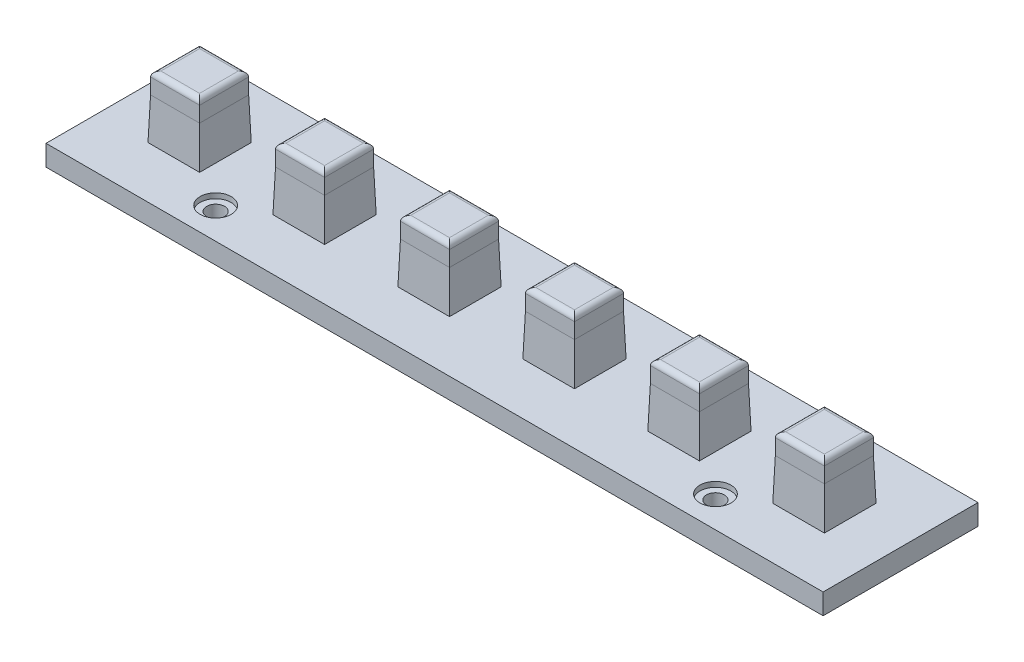
SolidWorks part; units mm, degrees
ref_plane "Front Plane" through (0, 0, 0) normal (0, 0, 1) x (1, 0, 0)
ref_plane "Top Plane" through (0, 0, 0) normal (0, 1, 0) x (1, 0, 0)
ref_plane "Right Plane" through (0, 0, 0) normal (1, 0, 0) x (0, 0, -1)
sketch "Sketch1" plane through (0, 0, 0) normal (0, 1, 0) x (1, 0, 0)
  line L0 (0, 15) -> (14.75, 15) construction
  line L1 (0, 0) -> (150.5, 0)
  line L2 (0, 0) -> (0, 30)
  line L3 (0, 30) -> (150.5, 30)
  line L4 (150.5, 0) -> (150.5, 30)
  line L5 (0, 0) -> (150.5, 30) construction
  line L6 (0, 30) -> (150.5, 0) construction
  line L7 (14.75, 15) -> (38.95, 15) construction
  line L8 (38.95, 15) -> (63.15, 15) construction
  line L9 (63.15, 15) -> (87.35, 15) construction
  line L10 (87.35, 15) -> (111.55, 15) construction
  line L11 (111.55, 15) -> (135.75, 15) construction
  line L14 (10, 19.75) -> (19.5, 19.75)
  line L15 (10, 19.75) -> (10, 10.25)
  line L16 (10, 10.25) -> (19.5, 10.25)
  line L17 (19.5, 19.75) -> (19.5, 10.25)
  line L18 (10, 19.75) -> (19.5, 10.25) construction
  line L19 (10, 10.25) -> (19.5, 19.75) construction
  line L24 (34.2, 19.75) -> (43.7, 19.75)
  line L25 (34.2, 19.75) -> (34.2, 10.25)
  line L26 (34.2, 10.25) -> (43.7, 10.25)
  line L27 (43.7, 19.75) -> (43.7, 10.25)
  line L28 (34.2, 19.75) -> (43.7, 10.25) construction
  line L29 (34.2, 10.25) -> (43.7, 19.75) construction
  line L30 (58.4, 19.75) -> (67.9, 19.75)
  line L31 (58.4, 19.75) -> (58.4, 10.25)
  line L32 (58.4, 10.25) -> (67.9, 10.25)
  line L33 (67.9, 19.75) -> (67.9, 10.25)
  line L34 (58.4, 19.75) -> (67.9, 10.25) construction
  line L35 (58.4, 10.25) -> (67.9, 19.75) construction
  line L36 (82.6, 19.75) -> (92.1, 19.75)
  line L37 (82.6, 19.75) -> (82.6, 10.25)
  line L38 (82.6, 10.25) -> (92.1, 10.25)
  line L39 (92.1, 19.75) -> (92.1, 10.25)
  line L40 (82.6, 19.75) -> (92.1, 10.25) construction
  line L41 (82.6, 10.25) -> (92.1, 19.75) construction
  line L42 (106.8, 19.75) -> (116.3, 19.75)
  line L43 (106.8, 19.75) -> (106.8, 10.25)
  line L44 (106.8, 10.25) -> (116.3, 10.25)
  line L45 (116.3, 19.75) -> (116.3, 10.25)
  line L46 (106.8, 19.75) -> (116.3, 10.25) construction
  line L47 (106.8, 10.25) -> (116.3, 19.75) construction
  line L48 (140.5, 19.75) -> (131, 19.75)
  line L49 (140.5, 19.75) -> (140.5, 10.25)
  line L50 (140.5, 10.25) -> (131, 10.25)
  line L51 (131, 19.75) -> (131, 10.25)
  line L52 (140.5, 19.75) -> (131, 10.25) construction
  line L53 (140.5, 10.25) -> (131, 19.75) construction
  line L54 (135.75, 15) -> (150.5, 15) construction
  point P4 (75.25, 15)
  point P14 (0, 15)
  point P18 (14.75, 15)
  point P24 (38.95, 15)
  point P28 (63.15, 15)
  point P33 (87.35, 15)
  point P38 (111.55, 15)
  point P43 (135.75, 15)
  point P44 (0, 0)
  point P45 (160.2994, 10.25)
  point P47 (0, 0)
  point P48 (0, 0)
  point P56 (135.75, 15)
  dimension "D1" = 9.5
  dimension "D2" = 24.2
  dimension "D3" = 10
  dimension "D4" = 30
extrude "Boss-Extrude1" add sketch "Sketch1" along normal blind 4
sketch "Sketch2" plane through (0, 4, 0) normal (0, 1, 0) x (1, 0, 0)
  line L1 (10, 19.75) -> (19.5, 19.75)
  line L2 (10, 19.75) -> (10, 10.25)
  line L3 (10, 10.25) -> (19.5, 10.25)
  line L4 (19.5, 19.75) -> (19.5, 10.25)
  line L5 (10, 19.75) -> (19.5, 10.25) construction
  line L6 (10, 10.25) -> (19.5, 19.75) construction
  line L7 (34.2, 19.75) -> (43.7, 19.75)
  line L8 (34.2, 19.75) -> (34.2, 10.25)
  line L9 (34.2, 10.25) -> (43.7, 10.25)
  line L10 (43.7, 19.75) -> (43.7, 10.25)
  line L11 (34.2, 19.75) -> (43.7, 10.25) construction
  line L12 (34.2, 10.25) -> (43.7, 19.75) construction
  line L13 (58.4, 19.75) -> (67.9, 19.75)
  line L14 (58.4, 19.75) -> (58.4, 10.25)
  line L15 (58.4, 10.25) -> (67.9, 10.25)
  line L16 (67.9, 19.75) -> (67.9, 10.25)
  line L17 (58.4, 19.75) -> (67.9, 10.25) construction
  line L18 (58.4, 10.25) -> (67.9, 19.75) construction
  line L19 (82.6, 19.75) -> (92.1, 19.75)
  line L20 (82.6, 19.75) -> (82.6, 10.25)
  line L21 (82.6, 10.25) -> (92.1, 10.25)
  line L22 (92.1, 19.75) -> (92.1, 10.25)
  line L23 (82.6, 19.75) -> (92.1, 10.25) construction
  line L24 (82.6, 10.25) -> (92.1, 19.75) construction
  line L25 (106.8, 19.75) -> (116.3, 19.75)
  line L26 (106.8, 19.75) -> (106.8, 10.25)
  line L27 (106.8, 10.25) -> (116.3, 10.25)
  line L28 (116.3, 19.75) -> (116.3, 10.25)
  line L29 (106.8, 19.75) -> (116.3, 10.25) construction
  line L30 (106.8, 10.25) -> (116.3, 19.75) construction
  line L31 (140.5, 19.75) -> (131, 19.75)
  line L32 (140.5, 19.75) -> (140.5, 10.25)
  line L33 (140.5, 10.25) -> (131, 10.25)
  line L34 (131, 19.75) -> (131, 10.25)
  line L35 (140.5, 19.75) -> (131, 10.25) construction
  line L36 (140.5, 10.25) -> (131, 19.75) construction
  line L50 (19.5, 10.25) -> (19.5, 19.75) construction
  line L51 (10, 10.25) -> (19.5, 10.25) construction
  point P4 (14.75, 15)
  point P9 (38.95, 15)
  point P14 (63.15, 15)
  point P19 (87.35, 15)
  point P24 (111.55, 15)
  point P29 (135.75, 15)
extrude "Boss-Extrude2" add sketch "Sketch2" along normal blind 12 and the other way up to surface (4 mm away) other way up to face at (75.25, 0, -15)
fillet "Fillet1" radius 1 24 edges at (14.75, 16, -19.75) (19.5, 16, -15) (14.75, 16, -10.25) (10, 16, -15) (135.75, 16, -10.25) (131, 16, -15) (135.75, 16, -19.75) (140.5, 16, -15) (111.55, 16, -19.75) (116.3, 16, -15) (111.55, 16, -10.25) (106.8, 16, -15) (87.35, 16, -19.75) (92.1, 16, -15) (87.35, 16, -10.25) (82.6, 16, -15) (63.15, 16, -19.75) (67.9, 16, -15) (63.15, 16, -10.25) (58.4, 16, -15) (38.95, 16, -19.75) (43.7, 16, -15) (38.95, 16, -10.25) (34.2, 16, -15)
chamfer "Chamfer1" distance 0.25 distance2 8 24 edges at (19.5, 4, -15) (14.75, 4, -19.75) (10, 4, -15) (14.75, 4, -10.25) (131, 4, -15) (135.75, 4, -10.25) (140.5, 4, -15) (135.75, 4, -19.75) (106.8, 4, -15) (111.55, 4, -10.25) (116.3, 4, -15) (111.55, 4, -19.75) (82.6, 4, -15) (87.35, 4, -10.25) (92.1, 4, -15) (87.35, 4, -19.75) (58.4, 4, -15) (63.15, 4, -10.25) (67.9, 4, -15) (63.15, 4, -19.75) (34.2, 4, -15) (38.95, 4, -10.25) (43.7, 4, -15) (38.95, 4, -19.75)
sketch "Sketch3" plane through (0, 4, 0) normal (0, 1, 0) x (1, 0, 0)
  line L0 (33.95, 10) -> (33.95, 20) construction
  line L3 (33.95, 15) -> (116.55, 15) construction
  line L4 (116.55, 20) -> (116.55, 10) construction
  line L5 (116.55, 15) -> (130.75, 15) construction
  line L6 (130.75, 10) -> (130.75, 20) construction
  line L7 (19.75, 15) -> (33.95, 15) construction
  line L8 (19.75, 20) -> (19.75, 10) construction
  line L9 (75.25, 15) -> (75.25, 30) construction
  line L10 (150.5, 30) -> (0, 30) construction
  line L11 (26.85, 6) -> (26.85, 15) construction
  line L12 (26.85, 15) -> (26.85, 24) construction
  circle A0 centre (26.85, 6) radius 1.725
  circle A1 centre (26.85, 24) radius 1.725
  circle A2 centre (123.65, 6) radius 1.725
  circle A3 centre (123.65, 24) radius 1.725
  dimension "D1" = 3.45
  dimension "D2" = 9
extrude "Cut-Extrude1" cut sketch "Sketch3" against normal through all
sketch "Sketch4" plane through (0, 4, 0) normal (0, 1, 0) x (1, 0, 0)
  circle A0 centre (26.85, 24) radius 3
  circle A1 centre (26.85, 6) radius 3
  circle A2 centre (123.65, 6) radius 3
  circle A3 centre (123.65, 24) radius 3
  dimension "D1" = 6
extrude "Cut-Extrude2" cut sketch "Sketch4" against normal blind 1
